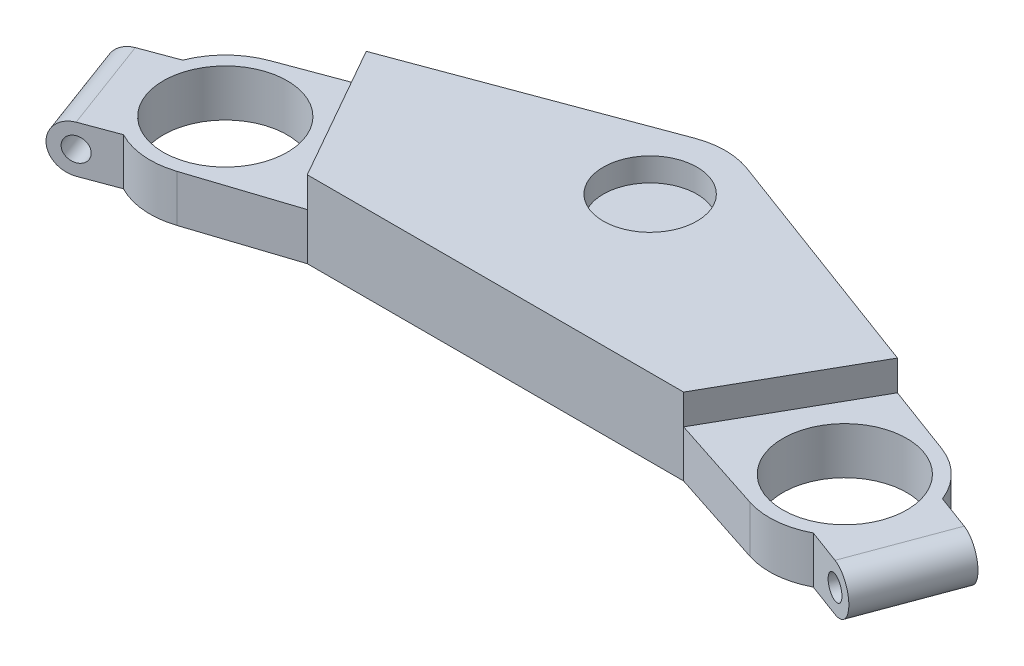
SolidWorks part; units mm, degrees
material "Cast Alloy Steel"
ref_plane "Front Plane" through (0, 0, 0) normal (0, 0, 1) x (1, 0, 0)
ref_plane "Top Plane" through (0, 0, 0) normal (0, 1, 0) x (1, 0, 0)
ref_plane "Right Plane" through (0, 0, 0) normal (1, 0, 0) x (0, 0, -1)
sketch "Sketch1" plane through (0, 0, 0) normal (0, 1, 0) x (1, 0, 0)
  line L14 (0, 0) -> (-92.5, -34.3665) construction
  line L15 (0, 0) -> (92.5, -34.3665) construction
  line L16 (0, 0) -> (0, -69.541) construction
  line L17 (-100.3361, -13.2752) -> (-7.8361, 21.0914)
  line L18 (-85.5247, -55.758) -> (-56.1961, -46.1946)
  line L19 (7.8361, 21.0914) -> (100.3361, -13.2752)
  line L20 (56.1961, -46.1946) -> (85.5247, -55.758)
  line L21 (-56.1961, -46.1946) -> (56.1961, -46.1946)
  line L23 (-92.5, -34.3665) -> (92.5, -34.3665) construction
  arc A1 (-100.3361, -13.2752) -> (-85.5247, -55.758) centre (-92.5, -34.3665) ccw
  arc A2 (85.5247, -55.758) -> (100.3361, -13.2752) centre (92.5, -34.3665) ccw
  arc A3 (7.8361, 21.0914) -> (-7.8361, 21.0914) centre (0, 0) ccw
  circle A4 centre (0, 0) radius 22.5 construction
  dimension "D1" = 45
  dimension "D2" = 185
  dimension "D6" = 45
  dimension "D7" = 45
extrude "Boss-Extrude1" add sketch "Sketch1" along normal blind 23 contours L19 A2 L20 L21 L18 A1 L17 A3
sketch "Sketch2" plane through (0, 23, 0) normal (0, 1, 0) x (1, 0, 0)
  circle A0 centre (-92.5, -34.3665) radius 18.51
  circle A1 centre (92.5, -34.3665) radius 18.51
  dimension "D1" = 37.02
  dimension "D2" = 37.02
extrude "Cut-Extrude1" cut sketch "Sketch2" against normal through all
sketch "Sketch3" plane through (0, 23, 0) normal (0, 1, 0) x (1, 0, 0)
  circle A0 centre (0, 0) radius 13.985
  dimension "D1" = 27.97
extrude "Cut-Extrude2" cut sketch "Sketch3" against normal blind 7
sketch "Sketch4" plane through (0, 23, 0) normal (0, 1, 0) x (1, 0, 0)
  line L0 (-113.4446, -26.1463) -> (-132.1925, -33.1117)
  line L1 (-132.1925, -33.1117) -> (-121.7444, -61.2335)
  line L2 (-121.7444, -61.2335) -> (-102.9965, -54.2681)
  line L3 (-100.3361, -13.2752) -> (-7.8361, 21.0914) construction
  line L4 (-126.9685, -47.1726) -> (-92.5, -34.3665) construction
  line L5 (0, 0) -> (-92.5, -34.3665) construction
  line L6 (-113.4446, -26.1463) -> (-102.9965, -54.2681) construction
  line L7 (0, 0) -> (0, -87.3927) construction
  line L11 (113.4446, -26.1463) -> (132.1925, -33.1117)
  line L12 (132.1925, -33.1117) -> (121.7444, -61.2335)
  line L13 (121.7444, -61.2335) -> (102.9965, -54.2681)
  arc A0 (-100.3361, -13.2752) -> (-85.5247, -55.758) centre (-92.5, -34.3665) ccw construction
  arc A1 (-113.4446, -26.1463) -> (-102.9965, -54.2681) centre (-92.5, -34.3665) ccw
  arc A4 (113.4446, -26.1463) -> (102.9965, -54.2681) centre (92.5, -34.3665) cw
  point P19 (-126.9685, -47.1726)
  dimension "D1" = 20
  dimension "D2" = 30
extrude "Boss-Extrude2" add sketch "Sketch4" against normal blind 23
sketch "Sketch5" plane through (5.2241, 0, 14.0609) normal (0.3483, 0, 0.9374) x (0.9374, 0, -0.3483)
  line L0 (-135.4483, 0) -> (-135.4483, 14)
  line L1 (-135.4483, 14) -> (-126.4483, 14)
  line L3 (-126.4483, 0) -> (-135.4483, 0)
  line L4 (-135.4483, 23) -> (-115.4483, 23) construction
  arc A0 (-126.4483, 14) -> (-126.4483, 0) centre (-126.4483, 7) ccw
  dimension "D1" = 7
  dimension "D2" = 9
  dimension "D3" = 9
  dimension "D4" = 9
extrude "Cut-Extrude3" cut sketch "Sketch5" against normal through all
sketch "Sketch10" plane through (5.2241, 0, 14.0609) normal (0.3483, 0, 0.9374) x (0.9374, 0, -0.3483)
  circle A0 centre (-126.4483, 7) radius 3.5
  dimension "D1" = 7
extrude "Cut-Extrude5" cut sketch "Sketch10" against normal blind 42
sketch "Sketch13" plane through (-5.2241, 0, 14.0609) normal (-0.3483, 0, 0.9374) x (0.9374, 0, 0.3483)
  line L1 (126.4483, 14) -> (135.4483, 14)
  line L2 (135.4483, 14) -> (135.4483, 0)
  line L3 (135.4483, 0) -> (126.4483, 0)
  line L4 (115.4483, 23) -> (135.4483, 23) construction
  arc A0 (126.4483, 14) -> (126.4483, 0) centre (126.4483, 7) cw
  dimension "D3" = 7
  dimension "D1" = 9
  dimension "D2" = 9
  dimension "D4" = 9
extrude "Cut-Extrude8" cut sketch "Sketch13" against normal through all
sketch "Sketch14" plane through (0, 23, 0) normal (0, 1, 0) x (1, 0, 0)
  line L0 (-56.1961, -46.1946) -> (-93.0338, 18.7025)
  line L1 (-93.0338, 18.7025) -> (-179.4836, -24.2361)
  line L2 (-179.4836, -24.2361) -> (-123.5385, -84.4203)
  line L3 (-123.5385, -84.4203) -> (-56.1961, -46.1946)
  line L4 (0, 0) -> (0, -90.0754) construction
  line L5 (179.4836, -24.2361) -> (123.5385, -84.4203)
  line L6 (93.0338, 18.7025) -> (179.4836, -24.2361)
  line L7 (56.1961, -46.1946) -> (93.0338, 18.7025)
  line L8 (123.5385, -84.4203) -> (56.1961, -46.1946)
extrude "Cut-Extrude9" cut sketch "Sketch14" against normal blind 9
sketch "Sketch15" plane through (-5.2241, 0, 14.0609) normal (-0.3483, 0, 0.9374) x (0.9374, 0, 0.3483)
  circle A0 centre (126.4483, 7) radius 3.5
  dimension "D1" = 7
extrude "Cut-Extrude10" cut sketch "Sketch15" against normal through all
